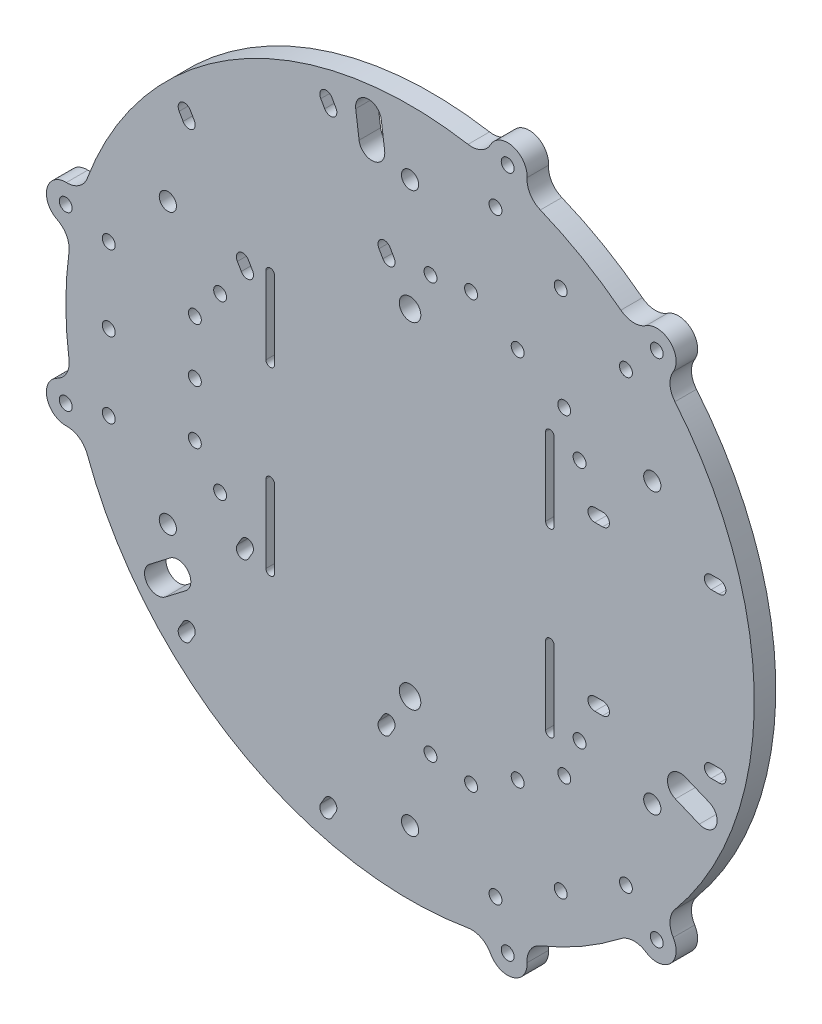
SolidWorks part; units mm, degrees
ref_plane "Front Plane" through (0, 0, 0) normal (0, 0, 1) x (1, 0, 0)
ref_plane "Top Plane" through (0, 0, 0) normal (0, 1, 0) x (1, 0, 0)
ref_plane "Right Plane" through (0, 0, 0) normal (1, 0, 0) x (0, 0, -1)
sketch "Sketch1" plane through (0, 0, 0) normal (0, 0, 1) x (1, 0, 0)
  circle A0 centre (0, 0) radius 80
  dimension "D1" = 160
extrude "Boss-Extrude1" add sketch "Sketch1" along normal blind 5
sketch "Sketch3" plane through (19.2768, 0, -52.9626) normal (0.342, 0, -0.9397) x (-0.9397, 0, -0.342)
  circle A0 centre (-67.48, -19) radius 1.5 construction
  circle A1 centre (-42.0511, -19) radius 1.5 construction
  circle A2 centre (-67.48, 19) radius 1.5 construction
  circle A3 centre (-42.0511, 19) radius 1.5 construction
  circle A4 centre (-67.48, -19) radius 1.5
  circle A5 centre (-42.0511, -19) radius 1.5
  circle A6 centre (-67.48, 19) radius 1.5
  circle A7 centre (-42.0511, 19) radius 1.5
extrude "Cut-Extrude1" cut sketch "Sketch3" against normal through all
sketch "Sketch4" plane through (0, 0, 0) normal (0, 0, -1) x (-1, 0, 0)
  line L0 (-71.8107, 20.5) -> (-69.9909, 20.5)
  line L1 (-71.8107, 17.5) -> (-69.9909, 17.5)
  line L2 (-44.7498, 20.5) -> (-42.93, 20.5)
  line L3 (-44.7498, 17.5) -> (-42.93, 17.5)
  line L4 (-71.8107, -17.5) -> (-69.9909, -17.5)
  line L5 (-71.8107, -20.5) -> (-69.9909, -20.5)
  line L6 (-44.7498, -17.5) -> (-42.93, -17.5)
  line L7 (-44.7498, -20.5) -> (-42.93, -20.5)
  ellipse E0 centre (-44.7498, 19) end of major axis (-46.3461, 19) minor radius 1.5 construction
  ellipse E1 centre (-71.8107, 19) end of major axis (-73.407, 19) minor radius 1.5 construction
  ellipse E2 centre (-71.8107, -19) end of major axis (-73.407, -19) minor radius 1.5 construction
  ellipse E3 centre (-44.7498, -19) end of major axis (-46.3461, -19) minor radius 1.5 construction
  ellipse E4 centre (-44.7498, 19) end of major axis (-46.3461, 19) minor radius 1.5
  ellipse E5 centre (-71.8107, 19) end of major axis (-73.407, 19) minor radius 1.5
  ellipse E6 centre (-71.8107, -19) end of major axis (-73.407, -19) minor radius 1.5
  ellipse E7 centre (-44.7498, -19) end of major axis (-46.3461, -19) minor radius 1.5
  ellipse E8 centre (-42.93, -19) end of major axis (-44.5262, -19) minor radius 1.5 construction
  ellipse E9 centre (-42.93, 19) end of major axis (-44.5262, 19) minor radius 1.5
  ellipse E10 centre (-42.93, 19) end of major axis (-44.5262, 19) minor radius 1.5
  ellipse E11 centre (-69.9909, 19) end of major axis (-71.5871, 19) minor radius 1.5
  ellipse E12 centre (-69.9909, 19) end of major axis (-71.5871, 19) minor radius 1.5
  ellipse E13 centre (-69.9909, -19) end of major axis (-71.5871, -19) minor radius 1.5
  ellipse E14 centre (-69.9909, -19) end of major axis (-71.5871, -19) minor radius 1.5
  ellipse E15 centre (-42.93, -19) end of major axis (-44.5262, -19) minor radius 1.5
  ellipse M4 centre (-44.7498, 19) end of major axis (-46.3461, 19) minor radius 1.5
  ellipse M5 centre (-71.8107, 19) end of major axis (-73.407, 19) minor radius 1.5
  ellipse M6 centre (-44.7498, -19) end of major axis (-46.3461, -19) minor radius 1.5
  ellipse M7 centre (-71.8107, -19) end of major axis (-73.407, -19) minor radius 1.5
  dimension "D1" = 0
  dimension "D2" = 0
  dimension "D3" = 0
extrude "Cut-Extrude2" cut sketch "Sketch4" against normal through all contours E6 E14 | E14 M7 | E6 E14 | E14 L4 M7 | E14 L5 M7 | E7 E15 | E7 E15 | E15 M6 | E15 L6 M6 | E15 L7 M6 | E4 E10 | E10 M4 | E4 E10 | E10 L2 M4 | E10 L3 M4 | E12 M5 | E5 E12 | E5 E12 | E12 L0 M5 | E12 L1 M5
pattern_circular "CirPattern1" count 3 over 360 of "Cut-Extrude2"
sketch "Sketch5" plane through (0, 0, 0) normal (0, 0, -1) x (-1, 0, 0)
  circle A0 centre (44.1435, 20) radius 1.5 construction
  circle A1 centre (44.1435, -20) radius 1.5 construction
  circle A2 centre (44.1435, 20) radius 1.5
  circle A3 centre (44.1435, -20) radius 1.5
extrude "Cut-Extrude3" cut sketch "Sketch5" against normal through all
pattern_circular "CirPattern2" count 3 over 360 about axis through (0, 0, 0) along (0, 0, 1) of "Cut-Extrude3"
sketch "Sketch6" plane through (0, 0, 0) normal (0, 0, -1) x (-1, 0, 0)
  line L0 (83.8316, 0) -> (96.3089, 0) construction
  line L1 (83.8316, -22.25) -> (83.8316, 22.25) construction
  line L2 (122.5, 0) -> (-122.5, 0) construction
  circle A0 centre (80.0198, -20) radius 4.5
  circle A1 centre (80.0198, -20) radius 1.5 construction
  circle A2 centre (80.0198, -20) radius 1.5
  circle A3 centre (80.0198, 20) radius 1.5
  circle A4 centre (80.0198, 20) radius 4.5
  dimension "D1" = 9
extrude "Boss-Extrude2" add sketch "Sketch6" against normal blind 5
fillet "Fillet1" radius 5 4 edges at (-76.6334, 22.9635, 2.5) (-78.4259, 15.7917, 2.5) (-78.4259, -15.7917, 2.5) (-76.6334, -22.9635, 2.5)
pattern_circular "CirPattern3" count 3 over 360 about axis through (0, 0, 0) along (0, 0, 1) of "Boss-Extrude2", "Fillet1"
sketch "Sketch7" plane through (0, 0, 5) normal (0, 0, 1) x (1, 0, 0)
  line L0 (-32.5, 30) -> (-32.5, 12) construction
  line L1 (-31.5, 30) -> (-31.5, 12)
  line L2 (-33.5, 30) -> (-33.5, 12)
  line L3 (-32.5, -12) -> (-32.5, -30) construction
  line L4 (-31.5, -12) -> (-31.5, -30)
  line L5 (-33.5, -12) -> (-33.5, -30)
  line L6 (32.5, -12) -> (32.5, -30) construction
  line L7 (33.5, -12) -> (33.5, -30)
  line L8 (31.5, -12) -> (31.5, -30)
  line L9 (32.5, 30) -> (32.5, 12) construction
  line L10 (33.5, 30) -> (33.5, 12)
  line L11 (31.5, 30) -> (31.5, 12)
  line L12 (-32.5, 12) -> (-32.5, -12) construction
  line L13 (-32.5, -30) -> (32.5, -30) construction
  line L14 (32.5, -12) -> (32.5, 12) construction
  line L15 (32.5, 30) -> (-32.5, 30) construction
  line L16 (-28.5, 35) -> (-28.5, -35) construction
  line L17 (28.5, -35) -> (28.5, 35) construction
  line L18 (-28.5, -35) -> (-9.5, -35) construction
  line L19 (-9.5, 35) -> (-28.5, 35) construction
  line L20 (0, 0) -> (0, 61.0239) construction
  line L21 (9.5, 35) -> (-9.5, 35) construction
  line L22 (-9.5, -35) -> (9.5, -35) construction
  arc A0 (-31.5, 30) -> (-33.5, 30) centre (-32.5, 30) ccw
  arc A1 (-33.5, 12) -> (-31.5, 12) centre (-32.5, 12) ccw
  arc A2 (-31.5, -12) -> (-33.5, -12) centre (-32.5, -12) ccw
  arc A3 (-33.5, -30) -> (-31.5, -30) centre (-32.5, -30) ccw
  arc A4 (33.5, -12) -> (31.5, -12) centre (32.5, -12) ccw
  arc A5 (31.5, -30) -> (33.5, -30) centre (32.5, -30) ccw
  arc A6 (33.5, 30) -> (31.5, 30) centre (32.5, 30) ccw
  arc A7 (31.5, 12) -> (33.5, 12) centre (32.5, 12) ccw
  circle A8 centre (0, 39) radius 2.5
  circle A9 centre (0, -39) radius 2.5
  point P2 (-32.5, 21)
  point P7 (-32.5, -21)
  point P14 (32.5, -21)
  point P21 (32.5, 21)
  dimension "D1" = 20
  dimension "D7" = 5
  dimension "D2" = 2
  dimension "D3" = 3
  dimension "D4" = 3
  dimension "D5" = 5
  dimension "D6" = 5
  dimension "D8" = 4
  dimension "D9" = 4
extrude "Cut-Extrude4" cut sketch "Sketch7" against normal through all
sketch "Sketch8" plane through (0, 0, 0) normal (0, 0, -1) x (-1, 0, 0)
  circle A0 centre (0, -65) radius 2 construction
  circle A1 centre (-56.2917, -32.5) radius 2 construction
  circle A2 centre (-56.2917, 32.5) radius 2 construction
  circle A3 centre (0, -65) radius 2
  circle A4 centre (-56.2917, -32.5) radius 2
  circle A5 centre (-56.2917, 32.5) radius 2
  circle A6 centre (56.2917, 32.5) radius 2 construction
  circle A7 centre (56.2917, -32.5) radius 2 construction
  circle A8 centre (56.2917, 32.5) radius 2
  circle A9 centre (56.2917, -32.5) radius 2
  circle A10 centre (0, 65) radius 2 construction
  circle A11 centre (0, 65) radius 2
extrude "Cut-Extrude5" cut sketch "Sketch8" against normal through all
sketch "Sketch9" plane through (0, 0, 0) normal (0, 0, -1) x (-1, 0, 0)
  line L0 (0, 0) -> (-73.9104, -30.6147) construction
  line L1 (-62.8238, -26.0225) -> (-68.3671, -28.3186) construction
  line L2 (-61.6758, -28.7941) -> (-67.219, -31.0902)
  line L3 (-63.9719, -23.2508) -> (-69.5151, -25.5469)
  line L4 (0, 0) -> (-87.5, 0) construction
  arc A0 (-61.5556, 51.097) -> (-61.5556, -51.097) centre (0, 0) ccw construction
  arc A1 (-61.6758, -28.7941) -> (-63.9719, -23.2508) centre (-62.8238, -26.0225) ccw
  arc A2 (-69.5151, -25.5469) -> (-67.219, -31.0902) centre (-68.3671, -28.3186) ccw
  point P8 (-65.5954, -27.1705)
  dimension "D2" = 12
  dimension "D1" = 6
  dimension "D3" = 3
  dimension "D4" = 22.5
extrude "Cut-Extrude6" cut sketch "Sketch9" against normal through all
pattern_circular "CirPattern4" count 3 over 360 about axis through (0, 0, 0) along (0, 0, 1) of "Cut-Extrude6"
sketch "Sketch10" plane through (0, 0, 0) normal (0, 0, -1) x (-1, 0, 0)
  line L0 (0, 0) -> (-22.6894, -79.2992) construction
  line L1 (0, 0) -> (-57.3304, -59.2992) construction
  line L2 (-19.8532, -69.3868) -> (-50.1641, -51.8868) construction
  line L3 (-14.1809, -49.562) -> (-35.8315, -37.062) construction
  line L4 (0, 0) -> (-35.0087, -60.6368) construction
  circle A0 centre (0, 0) radius 80 construction
  arc A1 (-13.4735, -78.8572) -> (75.0291, -27.7602) centre (0, 0) ccw construction
  circle A2 centre (-19.8532, -69.3868) radius 1.5
  circle A3 centre (-14.1809, -49.562) radius 1.5
  circle A4 centre (-50.1641, -51.8868) radius 1.5
  circle A5 centre (-35.8315, -37.062) radius 1.5
  circle A6 centre (-35.0087, -60.6368) radius 1.5
  circle A7 centre (-25.0062, -43.312) radius 1.5
  dimension "D1" = 3
  dimension "D2" = 35
  dimension "D3" = 25
extrude "Cut-Extrude7" cut sketch "Sketch10" against normal through all
pattern_circular "CirPattern5" count 3 over 360 about axis through (0, 0, 0) along (0, 0, 1) of "Cut-Extrude7"
